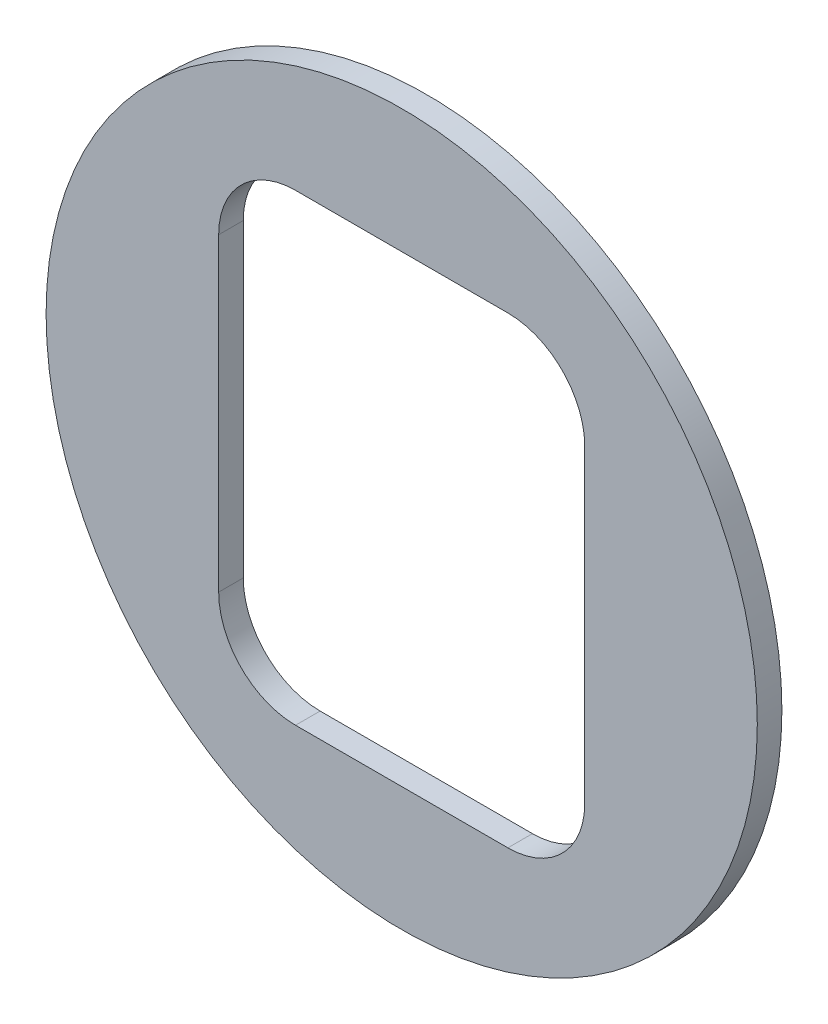
SolidWorks part; units mm, degrees
material "304, 316 OR 302 SSTL"
ref_plane "XY" through (0, 0, 0) normal (0, 0, 1) x (1, 0, 0)
ref_plane "XZ" through (0, 0, 0) normal (0, 1, 0) x (1, 0, 0)
ref_plane "YZ" through (0, 0, 0) normal (1, 0, 0) x (0, 0, -1)
sketch "Sketch1" plane through (0, 0, 0) normal (0, 0, 1) x (1, 0, 0)
  line L0 (-11.3411, 14.351) -> (11.3411, -14.351) construction
  line L1 (-11.3411, 14.351) -> (11.3411, 14.351)
  line L2 (-11.3411, 14.351) -> (-11.3411, -14.351)
  line L3 (-11.3411, -14.351) -> (11.3411, -14.351)
  line L4 (11.3411, 14.351) -> (11.3411, -14.351)
  circle A0 centre (0, 0) radius 22.0345
  dimension "D1" = 44.069
  dimension "D2" = 22.6822
  dimension "D3" = 28.702
extrude "Extrude1" add sketch "Sketch1" along normal blind 1.524
fillet "Fillet1" radius 4.7625 4 edges at (-11.3411, -14.351, 0.762) (11.3411, -14.351, 0.762) (11.3411, 14.351, 0.762) (-11.3411, 14.351, 0.762)
